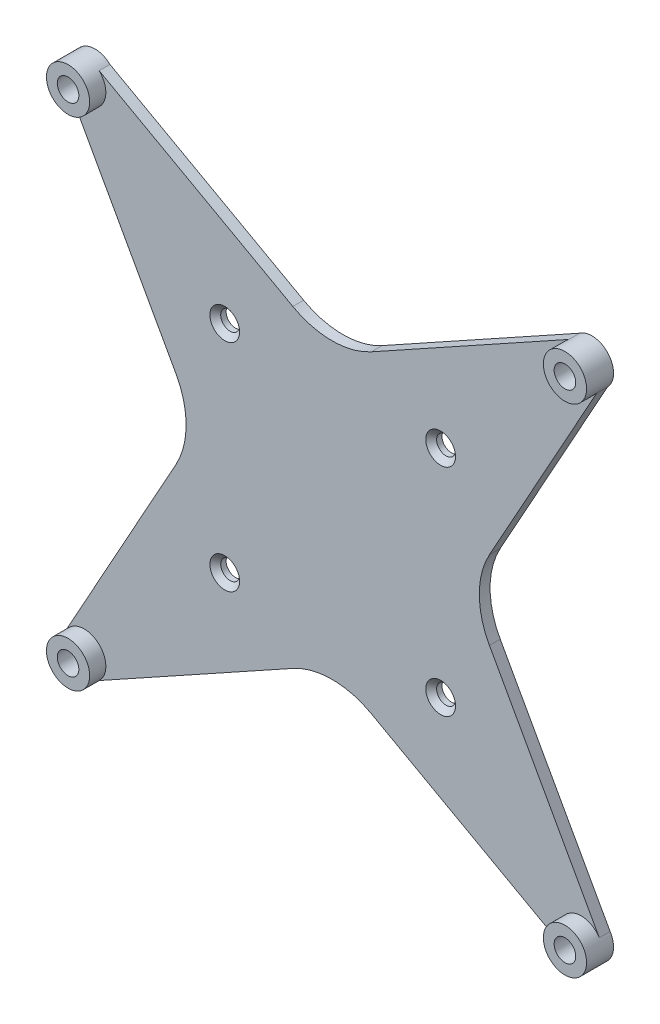
SolidWorks part; units mm, degrees
ref_plane "Front Plane" through (0, 0, 0) normal (0, 0, 1) x (1, 0, 0)
ref_plane "Top Plane" through (0, 0, 0) normal (0, 1, 0) x (1, 0, 0)
ref_plane "Right Plane" through (0, 0, 0) normal (1, 0, 0) x (0, 0, -1)
sketch "Sketch2" plane through (0, 0, 183.4071) normal (0, 0, -1) x (-1, 0, 0)
  circle A0 centre (-136.1545, 230.7932) radius 2
  circle A1 centre (-136.1545, 230.7932) radius 4
  circle A2 centre (-44.1544, 230.7932) radius 2
  circle A3 centre (-44.1544, 230.7932) radius 4
  circle A4 centre (-44.1544, 138.793) radius 2
  circle A5 centre (-44.1544, 138.793) radius 4
  circle A6 centre (-136.1545, 138.793) radius 2
  circle A7 centre (-136.1545, 138.793) radius 4
  dimension "D1" = 8
  dimension "D2" = 8
  dimension "D3" = 8
  dimension "D4" = 8
extrude "Boss-Extrude1" add sketch "Sketch2" along normal blind 5
sketch "Sketch3" plane through (0, 0, 178.4071) normal (0, 0, -1) x (-1, 0, 0)
  line L0 (-139.007, 227.989) -> (-115.1419, 184.9351)
  line L1 (-115.1419, 184.9351) -> (-139.5236, 140.9493)
  line L2 (-135.9297, 231.0772) -> (-135.9297, 138.793) construction
  line L3 (-133.857, 135.5186) -> (-90.042, 159.8057)
  line L4 (-90.042, 159.8057) -> (-46.919, 135.9022)
  line L5 (-135.9297, 138.793) -> (-44.1544, 138.793) construction
  line L6 (-40.7853, 140.9493) -> (-65.167, 184.9351)
  line L7 (-65.167, 184.9351) -> (-41.3019, 227.989)
  line L8 (-136.1545, 134.8057) -> (-44.1544, 134.8057) construction
  line L9 (-46.919, 233.684) -> (-90.042, 209.7805)
  line L10 (-90.042, 209.7805) -> (-133.857, 234.0676)
  line L12 (-140.1419, 230.7932) -> (-140.1419, 138.793) construction
  line L13 (-40.167, 138.793) -> (-40.167, 230.7932) construction
  line L14 (-44.1544, 234.7805) -> (-136.1545, 234.7805) construction
  circle A0 centre (-136.1545, 230.7932) radius 4 construction
  circle A1 centre (-136.1545, 138.793) radius 4 construction
  circle A2 centre (-44.1544, 138.793) radius 4 construction
  circle A3 centre (-44.1544, 230.7932) radius 4 construction
  arc A4 (-133.857, 234.0676) -> (-139.007, 227.989) centre (-136.1545, 230.7932) ccw
  arc A5 (-41.3019, 227.989) -> (-46.919, 233.684) centre (-44.1544, 230.7932) ccw
  arc A6 (-46.919, 135.9022) -> (-40.7853, 140.9493) centre (-44.1544, 138.793) ccw
  arc A7 (-139.5236, 140.9493) -> (-133.857, 135.5186) centre (-136.1545, 138.793) ccw
  point P32 (-135.9297, 184.9351)
  point P33 (-90.042, 138.793)
  point P34 (-40.9737, 228.3677)
  dimension "D1" = 25
  dimension "D2" = 25
  dimension "D3" = 25
  dimension "D4" = 25
  dimension "D5" = 29
  dimension "D6" = 29
  dimension "D7" = 29
  dimension "D8" = 29
  dimension "D9" = 29
  dimension "D10" = 29
  dimension "D11" = 29
  dimension "D12" = 29
extrude "Boss-Extrude2" add sketch "Sketch3" against normal blind 2
fillet "Fillet1" radius 15 4 edges at (90.042, 159.8057, 179.4071) (90.042, 209.7805, 179.4071) (65.167, 184.9351, 179.4071) (115.1419, 184.9351, 179.4071)
sketch "Sketch4" plane through (0, 0, 180.4071) normal (0, 0, 1) x (1, 0, 0)
  line L0 (40.167, 138.793) -> (40.167, 230.7932) construction
  line L1 (140.1419, 230.7932) -> (140.1419, 138.793) construction
  line L2 (136.1545, 134.8057) -> (44.1544, 134.8057) construction
  line L3 (44.1544, 234.7805) -> (136.1545, 234.7805) construction
  circle A0 centre (70.167, 204.7805) radius 1.75
  circle A1 centre (110.1419, 204.7805) radius 1.75
  circle A2 centre (110.1419, 164.8057) radius 1.75
  circle A3 centre (70.167, 164.8057) radius 1.75
  dimension "D1" = 3.5
  dimension "D2" = 3.5
  dimension "D3" = 3.5
  dimension "D4" = 3.5
  dimension "D5" = 30
  dimension "D6" = 30
  dimension "D7" = 30
  dimension "D8" = 30
extrude "Cut-Extrude1" cut sketch "Sketch4" against normal up to next
chamfer "Chamfer1" distance 1 angle 45 4 edges at (111.8919, 164.8057, 180.4071) (71.917, 164.8057, 180.4071) (111.8919, 204.7805, 180.4071) (71.917, 204.7805, 180.4071)
